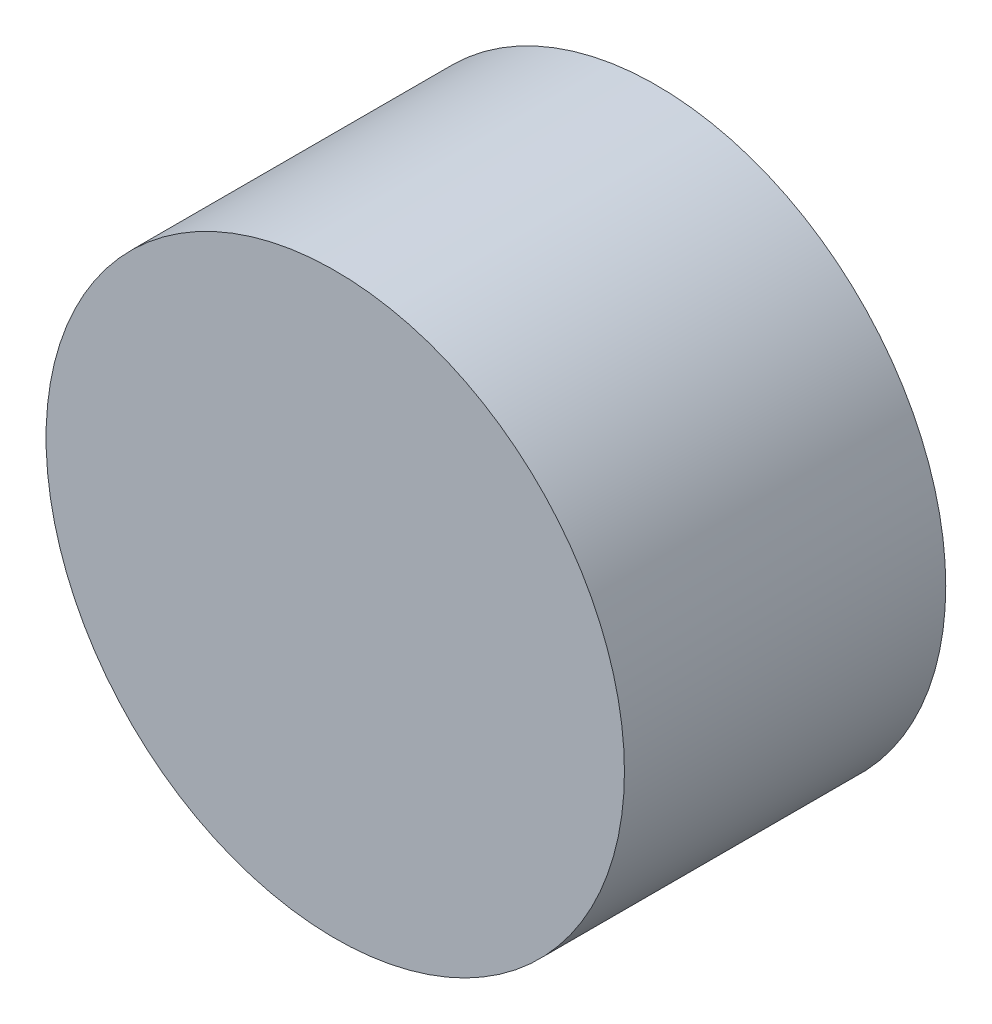
SolidWorks part; units mm, degrees
ref_plane "Front Plane" through (0, 0, 0) normal (0, 0, 1) x (1, 0, 0)
ref_plane "Top Plane" through (0, 0, 0) normal (0, 1, 0) x (1, 0, 0)
ref_plane "Right Plane" through (0, 0, 0) normal (1, 0, 0) x (0, 0, -1)
sketch "Sketch1" plane through (0, 0, 0) normal (0, 0, 1) x (1, 0, 0)
  circle A0 centre (0, 0) radius 9
  dimension "D1" = 18
extrude "Boss-Extrude1" add sketch "Sketch1" along normal blind 10
sketch "Sketch2" plane through (0, 0, 0) normal (0, 0, -1) x (-1, 0, 0)
  circle A0 centre (0, 0) radius 3
  dimension "D1" = 6
extrude "Cut-Extrude1" cut sketch "Sketch2" against normal blind 8
